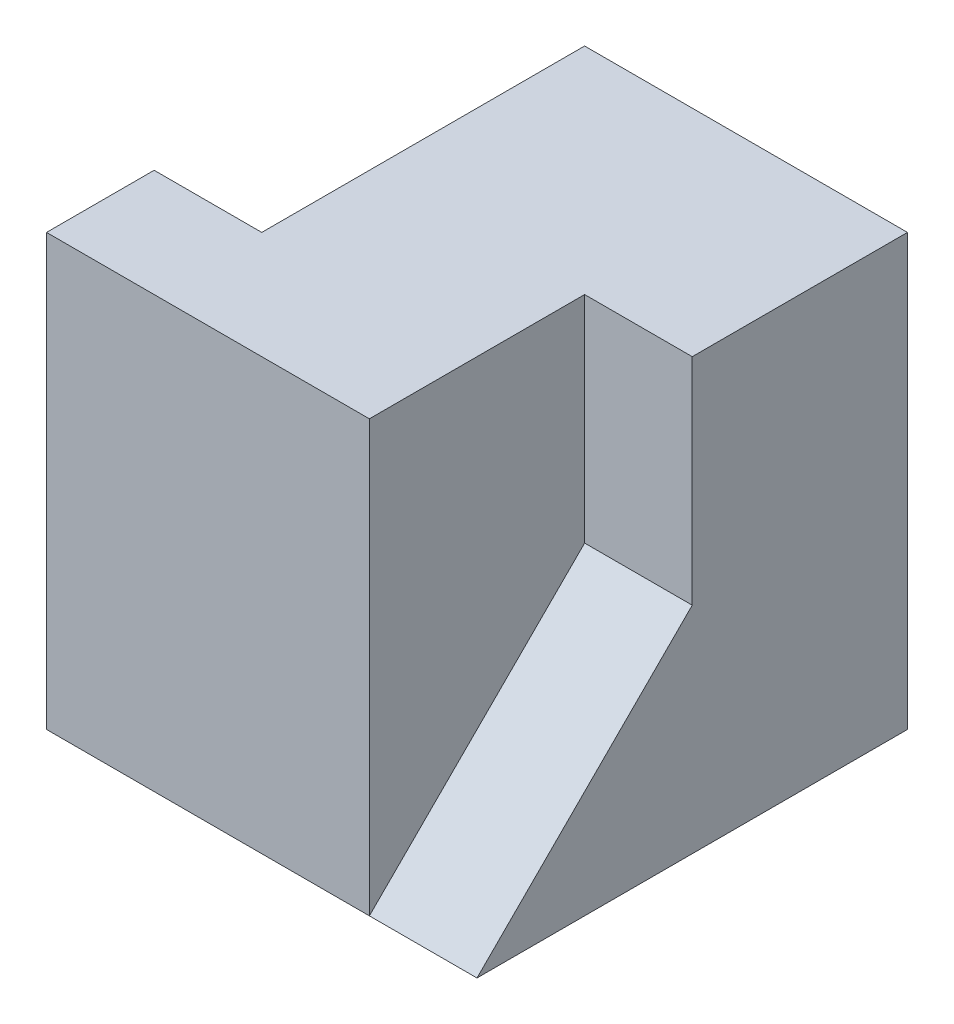
SolidWorks part; units mm, degrees
ref_plane "Front Plane" through (0, 0, 0) normal (0, 0, 1) x (1, 0, 0)
ref_plane "Top Plane" through (0, 0, 0) normal (0, 1, 0) x (1, 0, 0)
ref_plane "Right Plane" through (0, 0, 0) normal (1, 0, 0) x (0, 0, -1)
sketch "Sketch1" plane through (0, 0, 0) normal (0, 0, 1) x (1, 0, 0)
  line L1 (0, 0) -> (40, 0)
  line L2 (0, 0) -> (0, 40)
  line L3 (0, 40) -> (40, 40)
  line L4 (40, 0) -> (40, 40)
  dimension "D1" = 40
  dimension "D2" = 40
extrude "Boss-Extrude1" add sketch "Sketch1" along normal blind 40
sketch "Sketch2" plane through (0, 40, 0) normal (0, 1, 0) x (1, 0, 0)
  line L1 (0, 0) -> (10, 0)
  line L2 (0, 0) -> (0, -10)
  line L3 (0, -10) -> (10, -10)
  line L4 (10, 0) -> (10, -10)
  dimension "D1" = 10
  dimension "D2" = 10
extrude "Cut-Extrude1" cut sketch "Sketch2" against normal blind 40
sketch "Sketch6" plane through (0, 0, 40) normal (0, 0, 1) x (1, 0, 0)
  line L1 (40, 40) -> (30, 40)
  line L2 (40, 40) -> (40, 20)
  line L3 (40, 20) -> (30, 20)
  line L4 (30, 40) -> (30, 20)
  line L5 (40, 0) -> (30, 0)
  line L6 (40, 0) -> (40, 20)
  line L7 (40, 20) -> (30, 20)
  line L8 (30, 0) -> (30, 20)
  line M3 (40, 0) -> (40, 40)
  line M4 (40, 40) -> (0, 40)
  dimension "D1" = 10
  dimension "D2" = 20
extrude "Cut-Extrude4" cut sketch "Sketch6" against normal blind 20 contours L4 L3 M4 M3
sketch "Sketch7" plane through (0, 0, 40) normal (0, 0, 1) x (1, 0, 0)
  line L1 (40, 0) -> (30, 0)
  line L2 (40, 0) -> (40, 20)
  line L3 (40, 20) -> (30, 20)
  line L4 (30, 0) -> (30, 20)
extrude "Cut-Extrude5" cut sketch "Sketch7" against normal blind 10
sketch "Sketch12" plane through (0, 40, 0) normal (0, 1, 0) x (1, 0, 0)
  line L1 (0, -10) -> (10, -10)
  line L2 (0, -10) -> (0, -30)
  line L3 (0, -30) -> (10, -30)
  line L4 (10, -10) -> (10, -30)
  dimension "D1" = 10
  dimension "D2" = 20
extrude "Cut-Extrude11" cut sketch "Sketch12" against normal blind 10
sketch "Sketch13" plane through (0, 0, 30) normal (0, 0, 1) x (1, 0, 0)
  line L0 (30, 20) -> (40, 20)
  line L1 (40, 20) -> (40, 0)
  line L2 (40, 0) -> (30, 0)
  line L3 (30, 0) -> (30, 20)
extrude "Boss-Extrude4" add sketch "Sketch13" along normal blind 10
sketch "Sketch15" plane through (40, 0, 0) normal (1, 0, 0) x (0, 0, -1)
  line L0 (-20, 20) -> (-40, 0)
  line L1 (-40, 0) -> (-40, 20)
  line L2 (-40, 20) -> (-20, 20)
extrude "Cut-Extrude12" cut sketch "Sketch15" against normal blind 10
sketch "Sketch16" plane through (0, 0, 0) normal (-1, 0, 0) x (0, 0, 1)
  line L0 (10, 0) -> (30, 40)
  line L1 (30, 40) -> (40, 40)
  line L2 (10, 0) -> (40, 0)
  line L4 (40, 0) -> (40, 40)
  line L5 (30, 30) -> (25, 30)
  line L6 (10, 30) -> (30, 30) construction
  line L7 (30, 30) -> (30, 40)
  line M2 (30, 40) -> (30, 30)
  line M3 (30, 30) -> (10, 30)
extrude "Boss-Extrude5" add sketch "Sketch16" against normal blind 10 contours L0 M3 M2
sketch "Sketch17" plane through (0, 0, 0) normal (-1, 0, 0) x (0, 0, 1)
  line L0 (25, 30) -> (10, 0)
  line L1 (10, 0) -> (10, 30)
  line L2 (10, 30) -> (25, 30)
extrude "Cut-Extrude15" cut sketch "Sketch17" against normal blind 10
